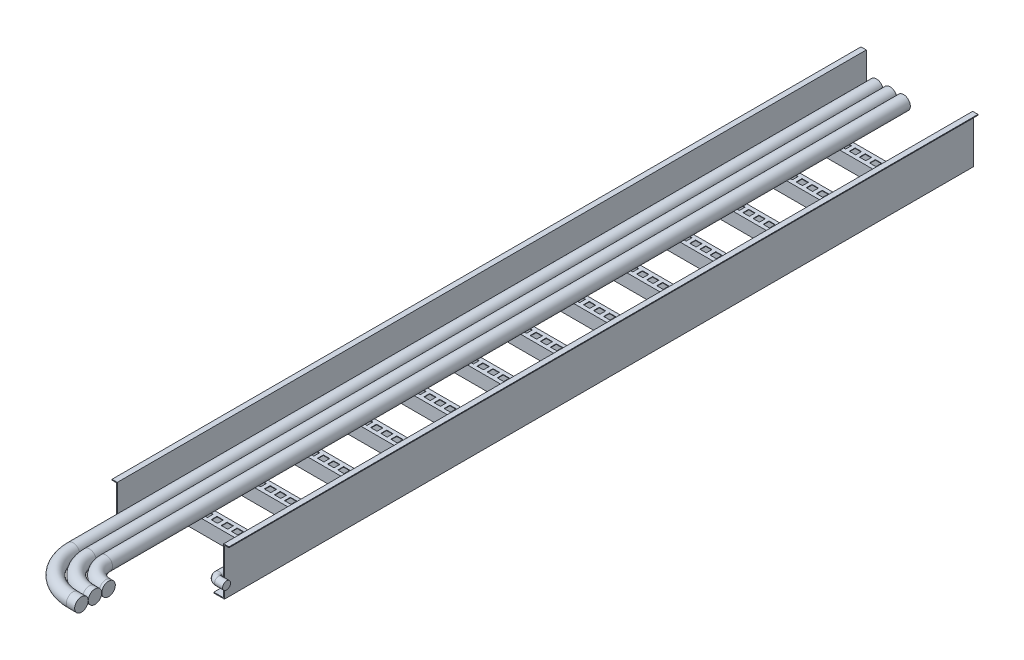
SolidWorks part; units mm, degrees
ref_plane "Alzado" through (0, 0, 0) normal (0, 0, 1) x (1, 0, 0)
ref_plane "Planta" through (0, 0, 0) normal (0, 1, 0) x (1, 0, 0)
ref_plane "Vista lateral" through (0, 0, 0) normal (1, 0, 0) x (0, 0, -1)
sketch "Croquis1" plane through (0, 0, 0) normal (0, 0, 1) x (1, 0, 0)
  line L0 (-55.6522, 76.1245) -> (-45.6522, 76.1245)
  line L1 (-45.6522, 76.1245) -> (-45.6522, -11.9155)
  line L2 (-45.6522, -11.9155) -> (154.3478, -11.9155)
  line L3 (154.3478, -11.9155) -> (154.3478, 76.1279)
  line L4 (154.3478, 76.1279) -> (164.3478, 76.1279)
  line L5 (164.3478, 76.1279) -> (164.3478, 74.6279)
  line L6 (164.3478, 74.6279) -> (155.8478, 74.6279)
  line L7 (155.8478, 74.6279) -> (155.8478, -13.4155)
  line L8 (155.8478, -13.4155) -> (-47.1522, -13.4155)
  line L9 (-47.1522, -13.4155) -> (-47.1522, 74.6245)
  line L10 (-47.1522, 74.6245) -> (-55.6522, 74.6245)
  line L11 (-55.6522, 74.6245) -> (-55.6522, 76.1245)
  line L12 (-27.1522, -11.9155) -> (-27.1522, -13.4155)
  line L13 (135.8478, -11.9155) -> (135.8478, -13.4155)
  dimension "D1" = 200
  dimension "D2" = 10
  dimension "D3" = 10
  dimension "D4" = 1.5
  dimension "D5" = 1.5
  dimension "D6" = 1.5
  dimension "D7" = 1.5
  dimension "D8" = 20
  dimension "D9" = 20
  dimension "D10" = 88.0435
  dimension "D11" = 88.04
  dimension "D12" = 1.5
extrude "Saliente-Extruir1" add sketch "Croquis1" along normal blind 1408.5 contours L2 L13 L8 L7 L6 L5 L4 L3 | L12 L2 L1 L0 L11 L10 L9 L8
sketch "Croquis2" plane through (155.8478, 0, 0) normal (1, 0, 0) x (0, 0, -1)
  line L1 (-125, -11.9155) -> (-124, -11.9155)
  line L2 (-125, -11.9155) -> (-125, 13.0845)
  line L3 (-125, 13.0845) -> (-100, 13.0845)
  line L4 (-100, -11.9155) -> (-100, 13.0845)
  line L5 (-125, -11.9155) -> (-100, 13.0845) construction
  line L6 (-125, 13.0845) -> (-100, -11.9155) construction
  line L7 (0, 74.6279) -> (0, -13.4155) construction
  line L8 (-124, -11.9155) -> (-124, 12.0845)
  line L9 (-124, 12.0845) -> (-101, 12.0845)
  line L10 (-101, 12.0845) -> (-101, -11.9155)
  line L11 (-101, -11.9155) -> (-100, -11.9155)
  point P0 (-112.5, 0.5845)
  point P9 (-237.5, 0.5845)
  point P16 (-362.5, 0.5845)
  dimension "D1" = 25
  dimension "D2" = 25
  dimension "D3" = 1
  dimension "D4" = 100
  dimension "D5" = 1
  dimension "D6" = 1
extrude "Saliente-Extruir2" add sketch "Croquis2" against normal up to surface (201.5 mm away) up to face at (-45.6522, 32.1045, 704.25)
pattern_linear "MatrizL1" count 13 spacing 100 along (0, 0, 1) of "Saliente-Extruir2"
sketch "Croquis3" plane through (0, 13.0845, 0) normal (0, 1, 0) x (1, 0, 0)
  line L0 (154.3478, -125) -> (154.3478, -100) construction
  line L1 (147.3478, -107) -> (135.3478, -107)
  line L2 (147.3478, -107) -> (147.3478, -118)
  line L3 (147.3478, -118) -> (135.3478, -118)
  line L4 (135.3478, -107) -> (135.3478, -118)
  line L5 (147.3478, -107) -> (135.3478, -118) construction
  line L6 (147.3478, -118) -> (135.3478, -107) construction
  line L7 (135.8478, -125) -> (154.3478, -125) construction
  line L8 (-45.6522, -100) -> (154.3478, -100) construction
  line L9 (-45.6522, -125) -> (154.3478, -125) construction
  line L10 (128.3478, -107) -> (116.3478, -107)
  line L11 (128.3478, -107) -> (128.3478, -118)
  line L12 (128.3478, -118) -> (116.3478, -118)
  line L13 (116.3478, -107) -> (116.3478, -118)
  line L14 (128.3478, -107) -> (116.3478, -118) construction
  line L15 (128.3478, -118) -> (116.3478, -107) construction
  line L17 (109.3478, -107) -> (97.3478, -107)
  line L18 (109.3478, -107) -> (109.3478, -118)
  line L19 (109.3478, -118) -> (97.3478, -118)
  line L20 (97.3478, -107) -> (97.3478, -118)
  line L21 (109.3478, -107) -> (97.3478, -118) construction
  line L22 (109.3478, -118) -> (97.3478, -107) construction
  line L23 (90.3478, -107) -> (78.3478, -107)
  line L24 (90.3478, -107) -> (90.3478, -118)
  line L25 (90.3478, -118) -> (78.3478, -118)
  line L26 (78.3478, -107) -> (78.3478, -118)
  line L27 (90.3478, -107) -> (78.3478, -118) construction
  line L28 (90.3478, -118) -> (78.3478, -107) construction
  line L29 (71.3478, -107) -> (59.3478, -107)
  line L30 (71.3478, -107) -> (71.3478, -118)
  line L31 (71.3478, -118) -> (59.3478, -118)
  line L32 (59.3478, -107) -> (59.3478, -118)
  line L33 (71.3478, -107) -> (59.3478, -118) construction
  line L34 (71.3478, -118) -> (59.3478, -107) construction
  line L35 (40.3478, -107) -> (52.3478, -107)
  line L36 (40.3478, -107) -> (40.3478, -118)
  line L37 (40.3478, -118) -> (52.3478, -118)
  line L38 (52.3478, -107) -> (52.3478, -118)
  line L39 (40.3478, -107) -> (52.3478, -118) construction
  line L40 (40.3478, -118) -> (52.3478, -107) construction
  line L41 (21.3478, -107) -> (33.3478, -107)
  line L42 (21.3478, -107) -> (21.3478, -118)
  line L43 (21.3478, -118) -> (33.3478, -118)
  line L44 (33.3478, -107) -> (33.3478, -118)
  line L45 (21.3478, -107) -> (33.3478, -118) construction
  line L46 (21.3478, -118) -> (33.3478, -107) construction
  line L47 (2.3478, -107) -> (14.3478, -107)
  line L48 (2.3478, -107) -> (2.3478, -118)
  line L49 (2.3478, -118) -> (14.3478, -118)
  line L50 (14.3478, -107) -> (14.3478, -118)
  line L51 (2.3478, -107) -> (14.3478, -118) construction
  line L52 (2.3478, -118) -> (14.3478, -107) construction
  line L53 (-16.6522, -107) -> (-4.6522, -107)
  line L54 (-16.6522, -107) -> (-16.6522, -118)
  line L55 (-16.6522, -118) -> (-4.6522, -118)
  line L56 (-4.6522, -107) -> (-4.6522, -118)
  line L57 (-16.6522, -107) -> (-4.6522, -118) construction
  line L58 (-16.6522, -118) -> (-4.6522, -107) construction
  line L59 (-35.6522, -107) -> (-23.6522, -107)
  line L60 (-35.6522, -107) -> (-35.6522, -118)
  line L61 (-35.6522, -118) -> (-23.6522, -118)
  line L62 (-23.6522, -107) -> (-23.6522, -118)
  line L63 (-35.6522, -107) -> (-23.6522, -118) construction
  line L64 (-35.6522, -118) -> (-23.6522, -107) construction
  point P0 (141.3478, -112.5)
  point P11 (122.3478, -112.5)
  point P18 (103.3478, -112.5)
  point P23 (84.3478, -112.5)
  point P28 (65.3478, -112.5)
  point P33 (46.3478, -112.5)
  point P38 (27.3478, -112.5)
  point P43 (8.3478, -112.5)
  point P48 (-10.6522, -112.5)
  point P53 (-29.6522, -112.5)
  dimension "D1" = 7
  dimension "D2" = 7
  dimension "D3" = 7
  dimension "D4" = 12
  dimension "D5" = 7
  dimension "D6" = 7
  dimension "D7" = 12
  dimension "D8" = 7
  dimension "D9" = 12
  dimension "D10" = 7
  dimension "D11" = 7
  dimension "D12" = 7
  dimension "D13" = 7
  dimension "D14" = 7
  dimension "D15" = 7
  dimension "D16" = 12
  dimension "D17" = 7
  dimension "D18" = 7
  dimension "D19" = 7
  dimension "D20" = 12
  dimension "D21" = 7
  dimension "D22" = 12
  dimension "D23" = 7
  dimension "D24" = 12
  dimension "D25" = 7
  dimension "D26" = 12
  dimension "D27" = 7
  dimension "D28" = 12
  dimension "D29" = 7
  dimension "D30" = 12
extrude "Cortar-Extruir1" cut sketch "Croquis3" against normal blind 25
pattern_linear "MatrizL2" count 50 spacing 100 along (0, 0, 1) of "Cortar-Extruir1"
sketch "Croquis4" plane through (0, 0, 0) normal (0, 0, -1) x (-1, 0, 0)
  line L0 (45.6522, 76.1245) -> (45.6522, -11.9155) construction
  line L1 (45.6522, 13.0845) -> (-154.3478, 13.0845) construction
  line L2 (-154.3478, -11.9155) -> (-154.3478, 76.1279) construction
  circle A0 centre (26.6022, 25.7845) radius 12.7
  circle A1 centre (1.1022, 25.7845) radius 12.7
  circle A2 centre (-24.3978, 25.7845) radius 12.7
  circle A3 centre (-146.3478, 20.5845) radius 7.5
  dimension "D1" = 25.4
  dimension "D4" = 25.4
  dimension "D6" = 25.4
  dimension "D8" = 15
  dimension "D2" = 19.05
  dimension "D3" = 12.7
  dimension "D5" = 25.5
  dimension "D7" = 25.5
  dimension "D9" = 7.5
  dimension "D10" = 8
extrude "Saliente-Extruir3" add sketch "Croquis4" against normal up to surface (1408.5 mm away) separate body up to face at (-43.9022, 31.3545, 1408.5)
sketch3d "Croquis3D1"
  line L0 (24.3978, 25.7845, 1408.5) -> (24.3978, 25.7845, 1499.95)
  line L1 (24.3978, 25.7845, 1408.5) -> (24.3978, 25.7845, 0) construction
  line L2 (64.3978, 25.7845, 1539.95) -> (69.3478, 25.7845, 1539.95)
  arc A0 (24.3978, 25.7845, 1499.95) -> (64.3978, 25.7845, 1539.95) centre (64.3978, 25.7845, 1499.95) ccw
  point P7 (24.3978, 25.7845, 1539.95)
  point P8 (64.3978, 65.7845, 1499.95)
  dimension "D3" = 40
  dimension "D1" = 131.45
  dimension "D2" = 44.95
sketch "Croquis5" plane through (0, 0, 1408.5) normal (0, 0, 1) x (1, 0, 0)
  circle A0 centre (24.3978, 25.7845) radius 12.7
sweep "Barrer1" add profiles "Croquis5" path "Croquis3D1"
sketch3d "Croquis3D2"
  line L0 (-1.1022, 25.7845, 1408.5) -> (-1.1022, 25.7845, 1505.35)
  line L1 (-1.1022, 25.7845, 1408.5) -> (-1.1022, 25.7845, 0) construction
  line L2 (58.8978, 25.7845, 1565.35) -> (69.2478, 25.7845, 1565.35)
  arc A0 (-1.1022, 25.7845, 1505.35) -> (58.8978, 25.7845, 1565.35) centre (58.8978, 25.7845, 1505.35) ccw
  point P7 (-1.1022, 25.7845, 1565.35)
  point P8 (58.8978, 85.7845, 1505.35)
  dimension "D3" = 60
  dimension "D1" = 156.85
  dimension "D2" = 70.35
sketch "Croquis6" plane through (0, 0, 1408.5) normal (0, 0, 1) x (1, 0, 0)
  circle A0 centre (-1.1022, 25.7845) radius 12.7
sweep "Barrer2" add profiles "Croquis6" path "Croquis3D2"
sketch3d "Croquis3D3"
  line L0 (-26.6022, 25.7845, 1408.5) -> (-26.6022, 25.7845, 1510.75)
  line L1 (-26.6022, 25.7845, 1408.5) -> (-26.6022, 25.7845, 0) construction
  line L2 (53.3978, 25.7845, 1590.75) -> (69.1478, 25.7845, 1590.75)
  arc A0 (-26.6022, 25.7845, 1510.75) -> (53.3978, 25.7845, 1590.75) centre (53.3978, 25.7845, 1510.75) ccw
  point P7 (-26.6022, 25.7845, 1590.75)
  point P8 (53.3978, 105.7845, 1510.75)
  dimension "D3" = 80
  dimension "D1" = 182.25
  dimension "D2" = 95.75
sketch "Croquis7" plane through (0, 0, 1408.5) normal (0, 0, 1) x (1, 0, 0)
  circle A0 centre (-26.6022, 25.7845) radius 12.7
sweep "Barrer3" add profiles "Croquis7" path "Croquis3D3"
sketch3d "Croquis3D5"
  line L0 (146.3478, 20.5845, 1408.5) -> (146.3478, 20.5845, 1410)
  line L1 (146.3478, 20.5845, 1408.5) -> (146.3478, 20.5845, 0) construction
  line L2 (154.3478, 20.5845, 1418) -> (169.3478, 20.5845, 1418)
  arc A0 (146.3478, 20.5845, 1410) -> (154.3478, 20.5845, 1418) centre (154.3478, 20.5845, 1410) ccw
  point P7 (146.3478, 20.5845, 1418)
  point P8 (154.3478, 28.5845, 1410)
  dimension "D3" = 8
  dimension "D1" = 9.5
  dimension "D2" = 23
sketch "Croquis10" plane through (0, 0, 1408.5) normal (0, 0, 1) x (1, 0, 0)
  circle A0 centre (146.3478, 20.5845) radius 7.5
sweep "Barrer5" add profiles "Croquis10" path "Croquis3D5"
